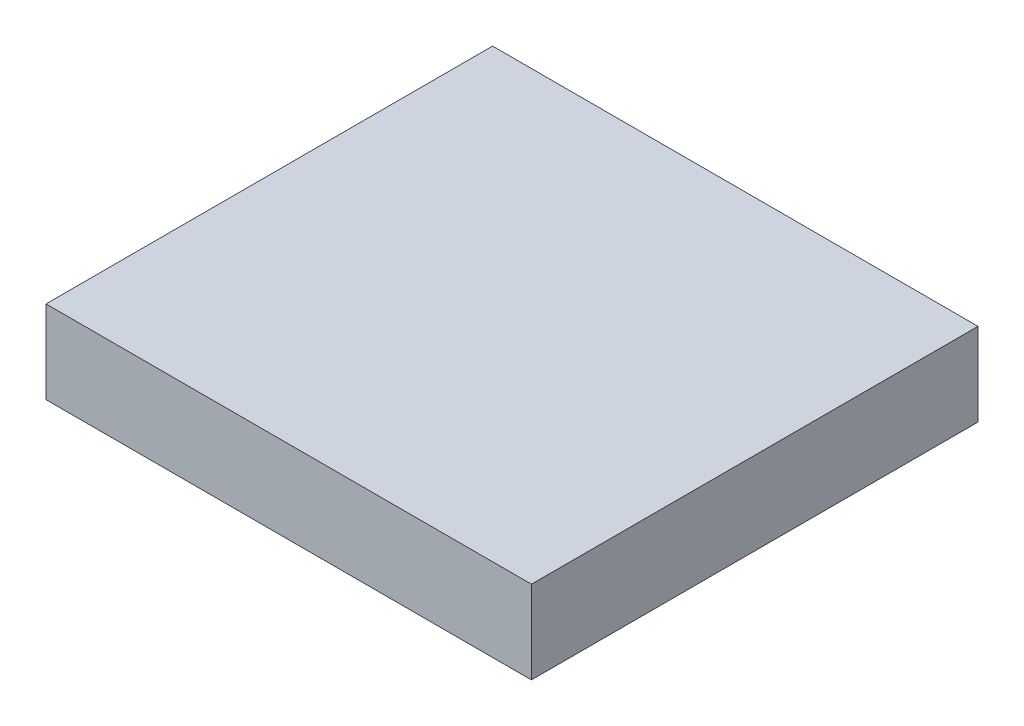
SolidWorks part; units mm, degrees
ref_plane "Front Plane" through (0, 0, 0) normal (0, 0, 1) x (1, 0, 0)
ref_plane "Top Plane" through (0, 0, 0) normal (0, 1, 0) x (1, 0, 0)
ref_plane "Right Plane" through (0, 0, 0) normal (1, 0, 0) x (0, 0, -1)
sketch "Sketch3" plane through (0, 0, 0) normal (0, 1, 0) x (1, 0, 0)
  line L0 (0, 0) -> (0, 35.7675) construction
  line L1 (0, 0) -> (-48.2343, 0) construction
  line L3 (-15.875, 14.605) -> (15.875, 14.605)
  line L4 (-15.875, 14.605) -> (-15.875, -14.605)
  line L5 (-15.875, -14.605) -> (15.875, -14.605)
  line L6 (15.875, 14.605) -> (15.875, -14.605)
  point P0 (0, 14.605)
  point P1 (-15.875, 0)
  dimension "D1" = 0
  dimension "D4" = 0
  dimension "D2" = 31.75
  dimension "D3" = 29.21
extrude "Boss-Extrude2" add sketch "Sketch3" along normal blind 5.4229
sketch "Sketch1" plane through (0, 0, 0) normal (0, 1, 0) x (1, 0, 0)
  line L0 (11.9677, 5.588) -> (11.9677, -5.588)
  line L1 (0, 0) -> (0, 78.5916) construction
  line L2 (0, 0) -> (-90.5086, 0) construction
  arc A1 (11.9677, 5.588) -> (11.9677, -5.588) centre (0, 0) ccw
  dimension "D1" = 11.176
  dimension "D2" = 13.208
  dimension "D3" = 0
  dimension "D4" = 0
extrude "Cut-Extrude1" cut sketch "Sketch1" along normal blind 0.8636
